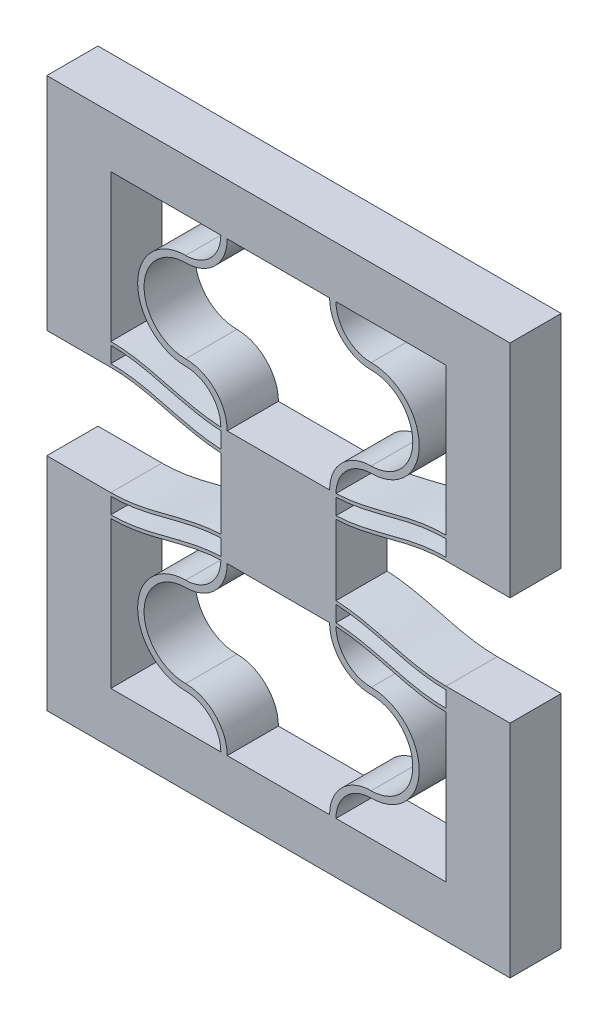
SolidWorks part; units mm, degrees
ref_plane "Front Plane" through (0, 0, 0) normal (0, 0, 1) x (1, 0, 0)
ref_plane "Top Plane" through (0, 0, 0) normal (0, 1, 0) x (1, 0, 0)
ref_plane "Right Plane" through (0, 0, 0) normal (1, 0, 0) x (0, 0, -1)
sketch "Sketch1" plane through (0, 0, 0) normal (0, 0, 1) x (1, 0, 0)
  line L4 (0, 11.5) -> (0, 0)
  line L5 (9.1, 0) -> (9.1, 13) construction
  line L6 (9.1, 13) -> (9.1, 15.9889) construction
  line L17 (8.6, 0) -> (0, 0)
  line L18 (9.6, 0) -> (18.2, 0)
  line L19 (18.2, 0) -> (18.2, 11.5)
  line L20 (9.6, 13.2389) -> (9.6, 14.4889)
  line L21 (8.6, 13.2389) -> (8.6, 14.4889)
  line L22 (9.6, 14.7389) -> (9.6, 15.9889)
  line L23 (9.6, 15.9889) -> (8.6, 15.9889)
  line L24 (8.6, 15.9889) -> (8.6, 14.7389)
  line L31 (-5, 13.25) -> (-5, -4)
  line L32 (-5, -4) -> (23.2, -4)
  line L33 (23.2, -4) -> (23.2, 13.25)
  line L34 (0, 11.75) -> (0, 13)
  line L36 (-5, 13.25) -> (0, 13.25)
  line L37 (23.2, 13.25) -> (18.2, 13.25)
  line L38 (18.2, 11.75) -> (18.2, 13)
  arc A0 (9.1, 13) -> (5.85, 9.75) centre (5.85, 13) cw
  arc A1 (5.85, 9.75) -> (5.85, 3.25) centre (5.85, 6.5) ccw
  arc A2 (5.85, 3.25) -> (9.1, 0) centre (5.85, 0) cw
  arc A3 (8.6, 12.9889) -> (5.85, 10.25) centre (5.85, 13) cw
  arc A4 (5.85, 10.25) -> (5.85, 2.75) centre (5.85, 6.5) ccw
  arc A5 (5.85, 2.75) -> (8.6, 0) centre (5.85, 0) cw
  arc A6 (8.6, 13) -> (5.85, 10.25) centre (5.85, 13) cw construction
  arc A7 (12.35, 3.25) -> (9.1, 0) centre (12.35, 0) ccw
  arc A8 (12.35, 2.75) -> (9.6, 0) centre (12.35, 0) ccw
  arc A9 (12.35, 9.75) -> (12.35, 3.25) centre (12.35, 6.5) cw
  arc A10 (12.35, 10.25) -> (12.35, 2.75) centre (12.35, 6.5) cw
  arc A11 (9.6, 12.9889) -> (12.35, 10.25) centre (12.35, 13) ccw
  arc A12 (9.1, 13) -> (12.35, 9.75) centre (12.35, 13) ccw
  spline S0 degree 4 poles (-1.8199, 11.8932) (-1.7916, 11.8889) (-1.7349, 11.8804) (-1.6205, 11.8641) (-1.4512, 11.8414) (-1.2773, 11.8213) (-1.1096, 11.8038) (-0.9328, 11.7885) (-0.7741, 11.7754) (-0.5529, 11.7634) (-0.3636, 11.7542) (-0.0324, 11.749) (0.0949, 11.7499) (0.4314, 11.7559) (0.588, 11.7659) (0.7922, 11.7766) (0.9923, 11.7932) (1.2619, 11.8181) (1.5583, 11.8543) (1.9616, 11.9128) (2.4135, 11.9926) (2.9515, 12.1031) (3.5687, 12.2482) (4.3822, 12.4549) (5.3319, 12.7054) (6.2874, 12.9364) (7.2543, 13.1135) (8.0575, 13.2104) (8.752, 13.2536) (9.4479, 13.2536) (10.1425, 13.2104) (10.9456, 13.1135) (11.9129, 12.9364) (12.8677, 12.7054) (13.8183, 12.4549) (14.5609, 12.2659) (15.0406, 12.1523) (15.4875, 12.0536) (15.8608, 11.9802) (16.2331, 11.9128) (16.6485, 11.8543) (16.9695, 11.813) (17.3577, 11.7813) (17.634, 11.7599) (18.1364, 11.7483) (18.2901, 11.7493) (18.6602, 11.7571) (18.8363, 11.7685) (19.0347, 11.7794) (19.2147, 11.7953) (19.4553, 11.8179) (19.675, 11.8448) (19.8515, 11.8679) (19.9626, 11.8846) (20.0199, 11.8932) knots 0 0 0 0 0 0.005186 0.010373 0.020745 0.031118 0.036304 0.041491 0.051737 0.061984 0.072231 0.082478 0.098173 0.10602 0.113867 0.121715 0.129562 0.145257 0.160951 0.176646 0.202553 0.228461 0.25985 0.291239 0.354018 0.405832 0.437222 0.468611 0.5 0.531389 0.562778 0.594168 0.645982 0.708761 0.74015 0.771539 0.784493 0.797447 0.823354 0.839049 0.854743 0.870438 0.886133 0.901827 0.917522 0.938016 0.943139 0.948263 0.958509 0.968882 0.979255 0.989627 1 1 1 1 1 construction
  spline S1 degree 4 poles (0, 11.75) (0.0726, 11.75) (0.1777, 11.7514) (0.4314, 11.7559) (0.588, 11.7659) (0.7922, 11.7766) (0.9923, 11.7932) (1.2619, 11.8181) (1.5583, 11.8543) (1.9616, 11.9128) (2.4135, 11.9926) (2.9515, 12.1031) (3.5687, 12.2482) (4.3822, 12.4549) (5.3319, 12.7054) (6.2874, 12.9364) (7.2543, 13.1135) (8.0575, 13.2104) (8.752, 13.2536) (9.4479, 13.2536) (10.1425, 13.2104) (10.9456, 13.1135) (11.9129, 12.9364) (12.8677, 12.7054) (13.8183, 12.4549) (14.5609, 12.2659) (15.0406, 12.1523) (15.4875, 12.0536) (15.8608, 11.9802) (16.2331, 11.9128) (16.6485, 11.8543) (16.9695, 11.813) (17.3577, 11.7813) (17.634, 11.7599) (17.984, 11.7518) (18.1274, 11.75) (18.2, 11.75) knots 0.082478 0.082478 0.082478 0.082478 0.082478 0.098173 0.10602 0.113867 0.121715 0.129562 0.145257 0.160951 0.176646 0.202553 0.228461 0.25985 0.291239 0.354018 0.405832 0.437222 0.468611 0.5 0.531389 0.562778 0.594168 0.645982 0.708761 0.74015 0.771539 0.784493 0.797447 0.823354 0.839049 0.854743 0.870438 0.886133 0.901827 0.917522 0.917522 0.917522 0.917522 0.917522
  spline S2 degree 4 poles (-1.8199, 13.1432) (-1.7916, 13.1389) (-1.7349, 13.1304) (-1.6205, 13.1141) (-1.4512, 13.0914) (-1.2773, 13.0713) (-1.1096, 13.0538) (-0.9328, 13.0385) (-0.7741, 13.0254) (-0.5529, 13.0134) (-0.3636, 13.0042) (-0.0324, 12.999) (0.0949, 12.9999) (0.4314, 13.0059) (0.588, 13.0159) (0.7922, 13.0266) (0.9923, 13.0432) (1.2619, 13.0681) (1.5583, 13.1043) (1.9616, 13.1628) (2.4135, 13.2426) (2.9515, 13.3531) (3.5687, 13.4982) (4.3822, 13.7049) (5.3319, 13.9554) (6.2874, 14.1864) (7.2543, 14.3635) (8.0575, 14.4604) (8.752, 14.5036) (9.4479, 14.5036) (10.1425, 14.4604) (10.9456, 14.3635) (11.9129, 14.1864) (12.8677, 13.9554) (13.8183, 13.7049) (14.5609, 13.5159) (15.0406, 13.4023) (15.4875, 13.3036) (15.8608, 13.2302) (16.2331, 13.1628) (16.6485, 13.1043) (16.9695, 13.063) (17.3577, 13.0313) (17.634, 13.0099) (18.1364, 12.9983) (18.2901, 12.9993) (18.6602, 13.0071) (18.8363, 13.0185) (19.0347, 13.0294) (19.2147, 13.0453) (19.4553, 13.0679) (19.675, 13.0948) (19.8515, 13.1179) (19.9626, 13.1346) (20.0199, 13.1432) knots 0 0 0 0 0 0.005186 0.010373 0.020745 0.031118 0.036304 0.041491 0.051737 0.061984 0.072231 0.082478 0.098173 0.10602 0.113867 0.121715 0.129562 0.145257 0.160951 0.176646 0.202553 0.228461 0.25985 0.291239 0.354018 0.405832 0.437222 0.468611 0.5 0.531389 0.562778 0.594168 0.645982 0.708761 0.74015 0.771539 0.784493 0.797447 0.823354 0.839049 0.854743 0.870438 0.886133 0.901827 0.917522 0.938016 0.943139 0.948263 0.958509 0.968882 0.979255 0.989627 1 1 1 1 1 construction
  spline S3 degree 4 poles (0, 13) (0.0726, 13) (0.1777, 13.0014) (0.4314, 13.0059) (0.588, 13.0159) (0.7922, 13.0266) (0.9923, 13.0432) (1.2619, 13.0681) (1.5583, 13.1043) (1.9616, 13.1628) (2.4135, 13.2426) (2.9515, 13.3531) (3.5687, 13.4982) (4.3822, 13.7049) (5.3319, 13.9554) (6.2874, 14.1864) (7.2543, 14.3635) (8.0575, 14.4604) (8.752, 14.5036) (9.4479, 14.5036) (10.1425, 14.4604) (10.9456, 14.3635) (11.9129, 14.1864) (12.8677, 13.9554) (13.8183, 13.7049) (14.5609, 13.5159) (15.0406, 13.4023) (15.4875, 13.3036) (15.8608, 13.2302) (16.2331, 13.1628) (16.6485, 13.1043) (16.9695, 13.063) (17.3577, 13.0313) (17.634, 13.0099) (17.984, 13.0018) (18.1274, 13) (18.2, 13) knots 0.082478 0.082478 0.082478 0.082478 0.082478 0.098173 0.10602 0.113867 0.121715 0.129562 0.145257 0.160951 0.176646 0.202553 0.228461 0.25985 0.291239 0.354018 0.405832 0.437222 0.468611 0.5 0.531389 0.562778 0.594168 0.645982 0.708761 0.74015 0.771539 0.784493 0.797447 0.823354 0.839049 0.854743 0.870438 0.886133 0.901827 0.917522 0.917522 0.917522 0.917522 0.917522
  spline S4 degree 4 poles (-1.8199, 13.3932) (-1.7916, 13.3889) (-1.7349, 13.3804) (-1.6205, 13.3641) (-1.4512, 13.3414) (-1.2773, 13.3213) (-1.1096, 13.3038) (-0.9328, 13.2885) (-0.7741, 13.2754) (-0.5529, 13.2634) (-0.3636, 13.2542) (-0.0324, 13.249) (0.0949, 13.2499) (0.4314, 13.2559) (0.588, 13.2659) (0.7922, 13.2766) (0.9923, 13.2932) (1.2619, 13.3181) (1.5583, 13.3543) (1.9616, 13.4128) (2.4135, 13.4926) (2.9515, 13.6031) (3.5687, 13.7482) (4.3822, 13.9549) (5.3319, 14.2054) (6.2874, 14.4364) (7.2543, 14.6135) (8.0575, 14.7104) (8.752, 14.7536) (9.4479, 14.7536) (10.1425, 14.7104) (10.9456, 14.6135) (11.9129, 14.4364) (12.8677, 14.2054) (13.8183, 13.9549) (14.5609, 13.7659) (15.0406, 13.6523) (15.4875, 13.5536) (15.8608, 13.4802) (16.2331, 13.4128) (16.6485, 13.3543) (16.9695, 13.313) (17.3577, 13.2813) (17.634, 13.2599) (18.1364, 13.2483) (18.2901, 13.2493) (18.6602, 13.2571) (18.8363, 13.2685) (19.0347, 13.2794) (19.2147, 13.2953) (19.4553, 13.3179) (19.675, 13.3448) (19.8515, 13.3679) (19.9626, 13.3846) (20.0199, 13.3932) knots 0 0 0 0 0 0.005186 0.010373 0.020745 0.031118 0.036304 0.041491 0.051737 0.061984 0.072231 0.082478 0.098173 0.10602 0.113867 0.121715 0.129562 0.145257 0.160951 0.176646 0.202553 0.228461 0.25985 0.291239 0.354018 0.405832 0.437222 0.468611 0.5 0.531389 0.562778 0.594168 0.645982 0.708761 0.74015 0.771539 0.784493 0.797447 0.823354 0.839049 0.854743 0.870438 0.886133 0.901827 0.917522 0.938016 0.943139 0.948263 0.958509 0.968882 0.979255 0.989627 1 1 1 1 1 construction
  spline S5 degree 4 poles (0, 13.25) (0.0726, 13.25) (0.1777, 13.2514) (0.4314, 13.2559) (0.588, 13.2659) (0.7922, 13.2766) (0.9923, 13.2932) (1.2619, 13.3181) (1.5583, 13.3543) (1.9616, 13.4128) (2.4135, 13.4926) (2.9515, 13.6031) (3.5687, 13.7482) (4.3822, 13.9549) (5.3319, 14.2054) (6.2874, 14.4364) (7.2543, 14.6135) (8.0575, 14.7104) (8.752, 14.7536) (9.4479, 14.7536) (10.1425, 14.7104) (10.9456, 14.6135) (11.9129, 14.4364) (12.8677, 14.2054) (13.8183, 13.9549) (14.5609, 13.7659) (15.0406, 13.6523) (15.4875, 13.5536) (15.8608, 13.4802) (16.2331, 13.4128) (16.6485, 13.3543) (16.9695, 13.313) (17.3577, 13.2813) (17.634, 13.2599) (17.984, 13.2518) (18.1274, 13.25) (18.2, 13.25) knots 0.082478 0.082478 0.082478 0.082478 0.082478 0.098173 0.10602 0.113867 0.121715 0.129562 0.145257 0.160951 0.176646 0.202553 0.228461 0.25985 0.291239 0.354018 0.405832 0.437222 0.468611 0.5 0.531389 0.562778 0.594168 0.645982 0.708761 0.74015 0.771539 0.784493 0.797447 0.823354 0.839049 0.854743 0.870438 0.886133 0.901827 0.917522 0.917522 0.917522 0.917522 0.917522
  spline S8 degree 4 poles (-1.8199, 11.6432) (-1.7916, 11.6389) (-1.7349, 11.6304) (-1.6205, 11.6141) (-1.4512, 11.5914) (-1.2773, 11.5713) (-1.1096, 11.5538) (-0.9328, 11.5385) (-0.7741, 11.5254) (-0.5529, 11.5134) (-0.3636, 11.5042) (-0.0324, 11.499) (0.0949, 11.4999) (0.4314, 11.5059) (0.588, 11.5159) (0.7922, 11.5266) (0.9923, 11.5432) (1.2619, 11.5681) (1.5583, 11.6043) (1.9616, 11.6628) (2.4135, 11.7426) (2.9515, 11.8531) (3.5687, 11.9982) (4.3822, 12.2049) (5.3319, 12.4554) (6.2874, 12.6864) (7.2543, 12.8635) (8.0575, 12.9604) (8.752, 13.0036) (9.4479, 13.0036) (10.1425, 12.9604) (10.9456, 12.8635) (11.9129, 12.6864) (12.8677, 12.4554) (13.8183, 12.2049) (14.5609, 12.0159) (15.0406, 11.9023) (15.4875, 11.8036) (15.8608, 11.7302) (16.2331, 11.6628) (16.6485, 11.6043) (16.9695, 11.563) (17.3577, 11.5313) (17.634, 11.5099) (18.1364, 11.4983) (18.2901, 11.4993) (18.6602, 11.5071) (18.8363, 11.5185) (19.0347, 11.5294) (19.2147, 11.5453) (19.4553, 11.5679) (19.675, 11.5948) (19.8515, 11.6179) (19.9626, 11.6346) (20.0199, 11.6432) knots 0 0 0 0 0 0.005186 0.010373 0.020745 0.031118 0.036304 0.041491 0.051737 0.061984 0.072231 0.082478 0.098173 0.10602 0.113867 0.121715 0.129562 0.145257 0.160951 0.176646 0.202553 0.228461 0.25985 0.291239 0.354018 0.405832 0.437222 0.468611 0.5 0.531389 0.562778 0.594168 0.645982 0.708761 0.74015 0.771539 0.784493 0.797447 0.823354 0.839049 0.854743 0.870438 0.886133 0.901827 0.917522 0.938016 0.943139 0.948263 0.958509 0.968882 0.979255 0.989627 1 1 1 1 1 construction
  spline S9 degree 4 poles (0, 11.5) (0.0726, 11.5) (0.1777, 11.5014) (0.4314, 11.5059) (0.588, 11.5159) (0.7922, 11.5266) (0.9923, 11.5432) (1.2619, 11.5681) (1.5583, 11.6043) (1.9616, 11.6628) (2.4135, 11.7426) (2.9515, 11.8531) (3.5687, 11.9982) (4.3822, 12.2049) (5.3319, 12.4554) (6.2874, 12.6864) (7.2543, 12.8635) (8.0575, 12.9604) (8.752, 13.0036) (9.4479, 13.0036) (10.1425, 12.9604) (10.9456, 12.8635) (11.9129, 12.6864) (12.8677, 12.4554) (13.8183, 12.2049) (14.5609, 12.0159) (15.0406, 11.9023) (15.4875, 11.8036) (15.8608, 11.7302) (16.2331, 11.6628) (16.6485, 11.6043) (16.9695, 11.563) (17.3577, 11.5313) (17.634, 11.5099) (17.984, 11.5018) (18.1274, 11.5) (18.2, 11.5) knots 0.082478 0.082478 0.082478 0.082478 0.082478 0.098173 0.10602 0.113867 0.121715 0.129562 0.145257 0.160951 0.176646 0.202553 0.228461 0.25985 0.291239 0.354018 0.405832 0.437222 0.468611 0.5 0.531389 0.562778 0.594168 0.645982 0.708761 0.74015 0.771539 0.784493 0.797447 0.823354 0.839049 0.854743 0.870438 0.886133 0.901827 0.917522 0.917522 0.917522 0.917522 0.917522
  dimension "D4" = 0.25
  dimension "D6" = 4
  dimension "D1" = 13
  dimension "D2" = 0.5
  dimension "D3" = 0.25
  dimension "D7" = 5
  dimension "D8" = 18.2
  dimension "D5" = 1.5
extrude "Boss-Extrude1" add sketch "Sketch1" along normal blind 4
sketch "Sketch4" plane through (0, 15.9889, 0) normal (0, 1, 0) x (1, 0, 0)
  line L24 (9.6, 0) -> (8.6, 0)
  line L25 (8.6, 0) -> (8.6, -4)
  line L26 (9.6, 0) -> (8.6, 0)
  line L27 (9.6, -4) -> (9.6, 0)
  line L29 (8.6, 0) -> (8.6, -4)
  line L31 (9.6, -4) -> (9.6, 0)
  line L32 (8.6, -4) -> (9.6, -4)
  line L33 (8.6, -4) -> (9.6, -4)
  dimension "D1" = 0
extrude "Boss-Extrude2" add sketch "Sketch4" along normal blind 1.5
mirror "Mirror3" about plane through (0, 17.4889, 0) normal (0, 1, 0) of bodies 179
ref_plane "Plane1" through (9.1, 0, 0) normal (-1, 0, 0) x (0, 0, 1)
split "Split2" trim tools "Plane1" bodies to split 247 102 resulting bodies 225
sketch "Sketch7" plane through (9.1, 0, 0) normal (-1, 0, 0) x (0, 0, 1)
  line L4 (4, 34.9777) -> (4, 38.9777)
  line L12 (0, 13) -> (4, 13)
  line L13 (0, 13) -> (4, 13)
  line L14 (4, 13) -> (4, 21.9777)
  line L15 (4, 13) -> (4, 21.9777)
  line L20 (4, 0) -> (0, 0)
  line L22 (4, 0) -> (0, 0)
  line L23 (0, -4) -> (4, -4)
  line L27 (0, -4) -> (4, -4)
  line L31 (4, 21.9777) -> (0, 21.9777)
  line L32 (4, 21.9777) -> (0, 21.9777)
  line L33 (0, 21.9777) -> (0, 13)
  line L34 (0, 21.9777) -> (0, 13)
  line L36 (4, -4) -> (4, 0)
  line L38 (4, 34.9777) -> (4, 38.9777)
  line L39 (4, 34.9777) -> (4, 38.9777)
  line L40 (4, 38.9777) -> (0, 38.9777)
  line L41 (4, 38.9777) -> (0, 38.9777)
  line L46 (4, 34.9777) -> (4, 38.9777)
  line L51 (0, 38.9777) -> (0, 34.9777)
  line L52 (0, 38.9777) -> (0, 34.9777)
  line L53 (0, 34.9777) -> (4, 34.9777)
  line L54 (0, 34.9777) -> (4, 34.9777)
  line L55 (4, 38.9777) -> (0, 38.9777)
  line L57 (4, 38.9777) -> (0, 38.9777)
  line L59 (4, -4) -> (4, 0)
  line L60 (0, 0) -> (0, -4)
  line L61 (0, 0) -> (0, -4)
  line L62 (0, 38.9777) -> (0, 34.9777)
  line L63 (0, 38.9777) -> (0, 34.9777)
  line L64 (0, 34.9777) -> (4, 34.9777)
  line L65 (0, 34.9777) -> (4, 34.9777)
  dimension "D1" = 0
  dimension "D2" = 0
  dimension "D3" = 0
  dimension "D4" = 0
extrude "Boss-Extrude3" add sketch "Sketch7" along normal blind 4
mirror "Mirror2" about plane through (5.1, 0, 0) normal (-1, 0, 0) of bodies 226
